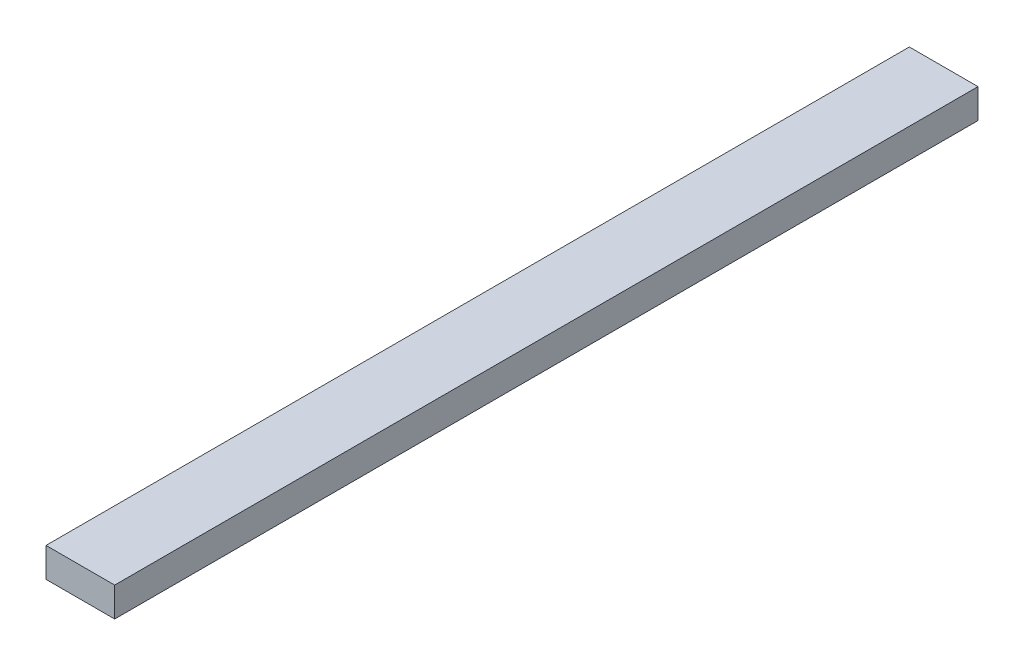
SolidWorks part; units mm, degrees
material "Pine"
ref_plane "Front Plane" through (0, 0, 0) normal (0, 0, 1) x (1, 0, 0)
ref_plane "Top Plane" through (0, 0, 0) normal (0, 1, 0) x (1, 0, 0)
ref_plane "Right Plane" through (0, 0, 0) normal (1, 0, 0) x (0, 0, -1)
sketch "Sketch1" plane through (0, 0, 0) normal (0, 0, 1) x (1, 0, 0)
  line L1 (0, 0) -> (88.9, 0)
  line L2 (0, 0) -> (0, 38.1)
  line L3 (0, 38.1) -> (88.9, 38.1)
  line L4 (88.9, 0) -> (88.9, 38.1)
  dimension "D1" = 88.9
  dimension "D2" = 38.1
extrude "Boss-Extrude1" add sketch "Sketch1" along normal blind 1117.6
